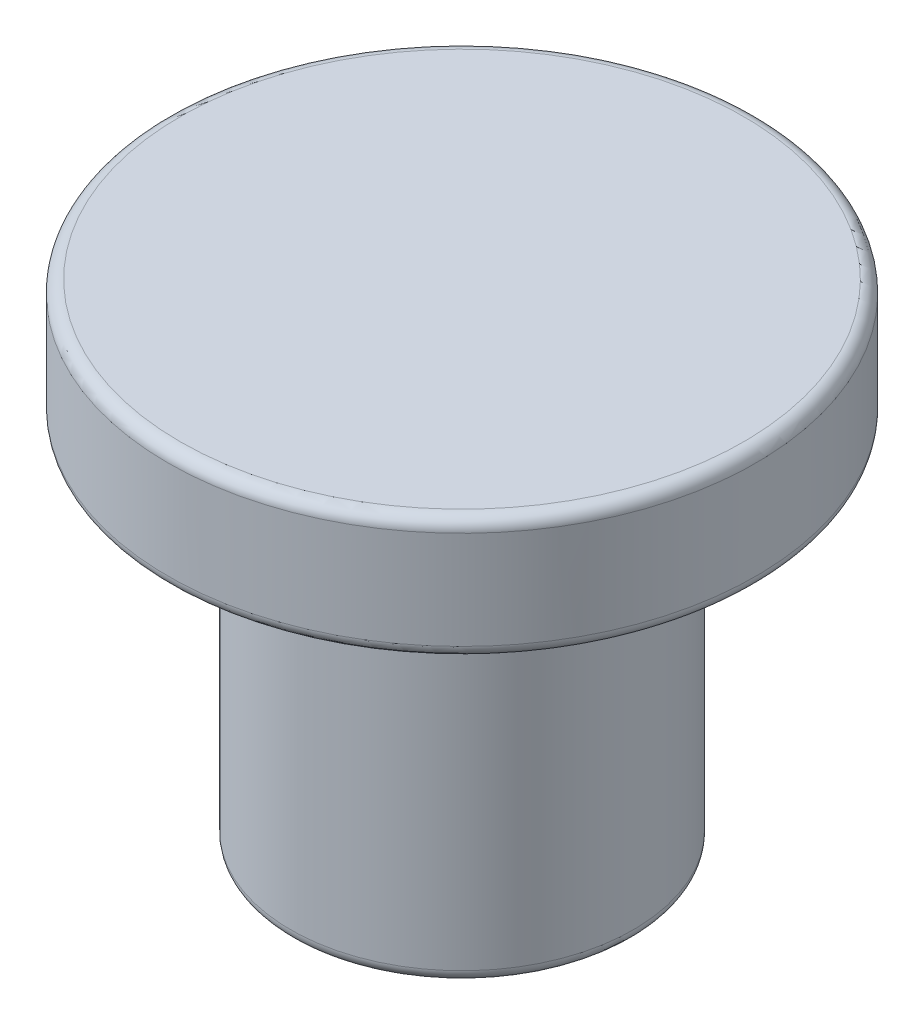
SolidWorks part; units mm, degrees
ref_plane "Plano frontal" through (0, 0, 0) normal (0, 0, 1) x (1, 0, 0)
ref_plane "Plano superior" through (0, 0, 0) normal (0, 1, 0) x (1, 0, 0)
ref_plane "Plano direito" through (0, 0, 0) normal (1, 0, 0) x (0, 0, -1)
sketch "Esboço1" plane through (0, 0, 0) normal (0, 0, 1) x (1, 0, 0)
  line L0 (0, 0) -> (0, 20)
  line L1 (0, 20) -> (12, 20)
  line L2 (12, 20) -> (12, 15)
  line L3 (12, 15) -> (7, 15)
  line L4 (7, 15) -> (7, 0)
  line L5 (7, 0) -> (0, 0)
  dimension "D1" = 7
  dimension "D2" = 12
  dimension "D3" = 5
  dimension "D4" = 20
revolve "Revolução1" add sketch "Esboço1" angle 360 about L0
fillet "Filete1" radius 0.5 3 edges at (0, 15, -12) (0, 20, -12) (0, 0, -7)
